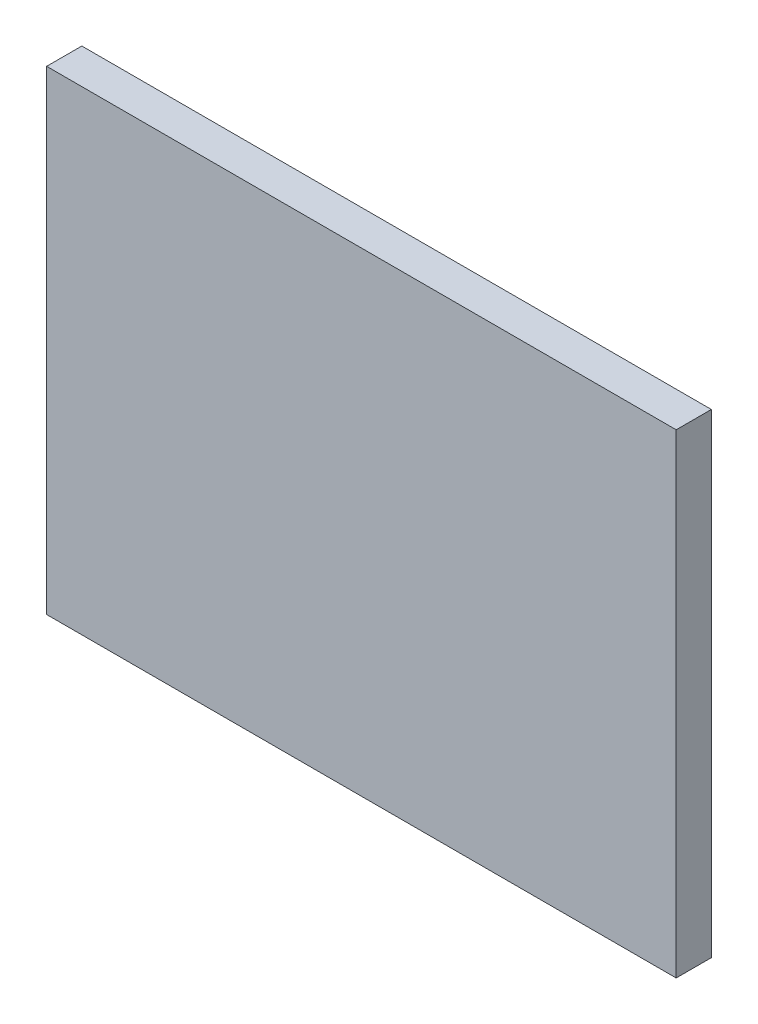
SolidWorks part; units mm, degrees
ref_plane "Front Plane" through (0, 0, 0) normal (0, 0, 1) x (1, 0, 0)
ref_plane "Top Plane" through (0, 0, 0) normal (0, 1, 0) x (1, 0, 0)
ref_plane "Right Plane" through (0, 0, 0) normal (1, 0, 0) x (0, 0, -1)
sketch "Sketch1" plane through (0, 0, 0) normal (0, 0, 1) x (1, 0, 0)
  line L1 (-17.9, 13.5) -> (17.9, 13.5)
  line L2 (-17.9, 13.5) -> (-17.9, -13.5)
  line L3 (-17.9, -13.5) -> (17.9, -13.5)
  line L4 (17.9, 13.5) -> (17.9, -13.5)
  line L5 (-17.9, 13.5) -> (17.9, -13.5) construction
  line L6 (-17.9, -13.5) -> (17.9, 13.5) construction
  point P0 (0, 0)
  dimension "D1" = 27
  dimension "D2" = 35.8
extrude "Boss-Extrude1" add sketch "Sketch1" along normal blind 2
